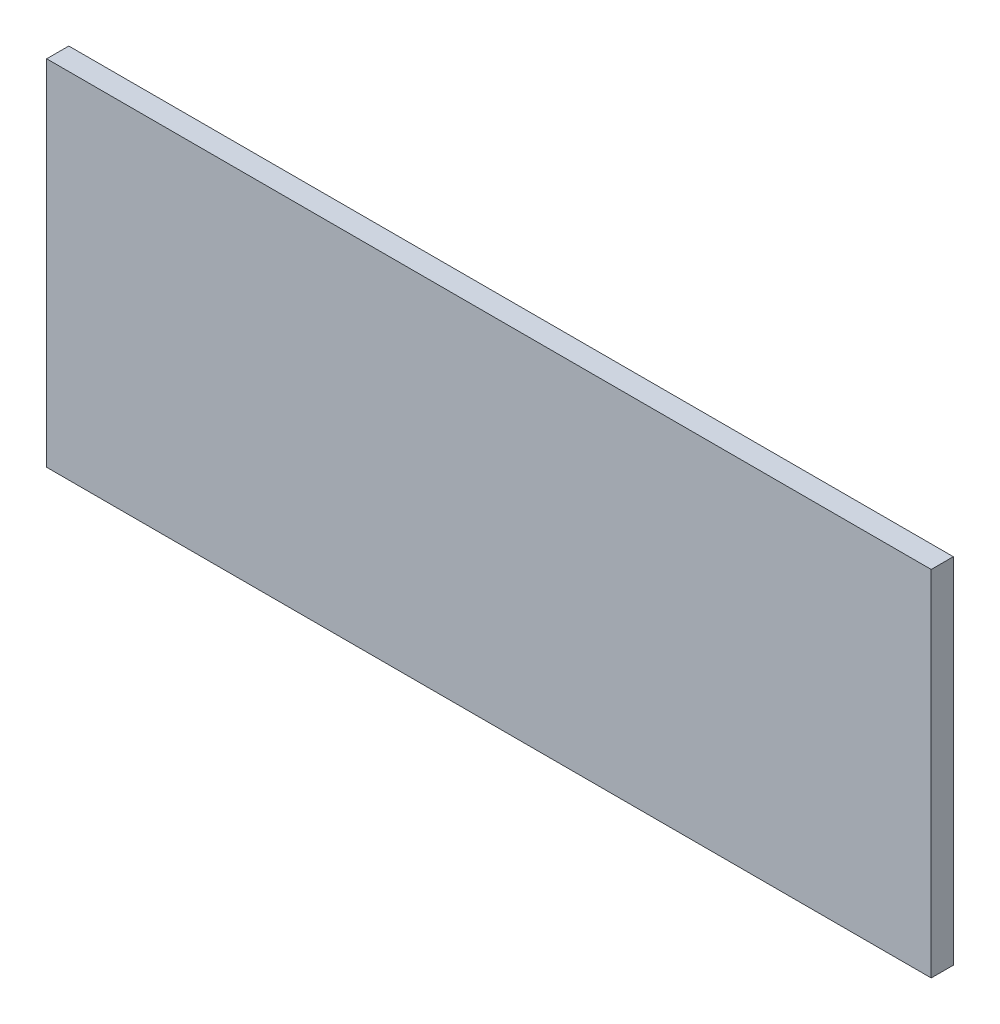
SolidWorks part; units mm, degrees
ref_plane "Front Plane" through (0, 0, 0) normal (0, 0, 1) x (1, 0, 0)
ref_plane "Top Plane" through (0, 0, 0) normal (0, 1, 0) x (1, 0, 0)
ref_plane "Right Plane" through (0, 0, 0) normal (1, 0, 0) x (0, 0, -1)
sketch "Sketch2" plane through (0, 0, 0) normal (0, 0, 1) x (1, 0, 0)
  line L1 (-63.5, -25.4) -> (63.5, -25.4)
  line L2 (-63.5, -25.4) -> (-63.5, 25.4)
  line L3 (-63.5, 25.4) -> (63.5, 25.4)
  line L4 (63.5, -25.4) -> (63.5, 25.4)
  line L5 (-63.5, -25.4) -> (63.5, 25.4) construction
  line L6 (-63.5, 25.4) -> (63.5, -25.4) construction
  point P0 (0, 0)
  dimension "D1" = 127
  dimension "D2" = 50.8
extrude "Boss-Extrude1" add sketch "Sketch2" along normal mid plane 3.175
